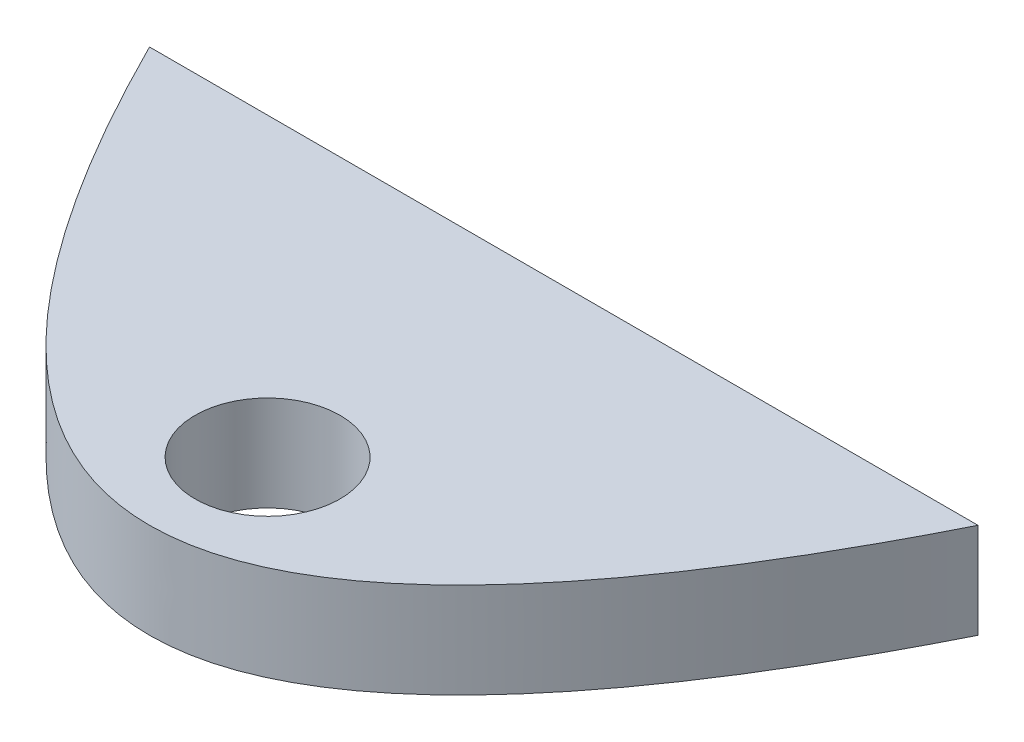
SolidWorks part; units mm, degrees
material "Custom Plastic (2)"
ref_plane "Front Plane" through (0, 0, 0) normal (0, 0, 1) x (1, 0, 0)
ref_plane "Top Plane" through (0, 0, 0) normal (0, 1, 0) x (1, 0, 0)
ref_plane "Right Plane" through (0, 0, 0) normal (1, 0, 0) x (0, 0, -1)
sketch "Sketch1" plane through (0, 0, 0) normal (0, 1, 0) x (1, 0, 0)
  line L0 (-200, 0) -> (200, 0)
  spline S0 degree 2 poles (-225.2396, 53.6645) (0, -453.6645) (225.2396, 53.6645) knots 0 0 0 1 1 1 construction
  spline S1 degree 2 poles (-200, 0) (0, -400) (200, 0) knots 0.056028 0.056028 0.056028 0.943972 0.943972 0.943972
extrude "Boss-Extrude1" add sketch "Sketch1" along normal blind 300
sketch "Sketch2" plane through (0, 300, 0) normal (0, 1, 0) x (1, 0, 0)
  line L0 (0, 200) -> (0, -200)
  line L2 (200, 0) -> (-200, 0) construction
  circle A0 centre (0, -143) radius 35
  parabola Q0 (-200, 0) -> (200, 0) focus (0, -150) apex (0, -200) construction
  point P4 (0, 0)
  dimension "D1" = 70
  dimension "D2" = 143
ref_plane "Plane1" through (0, 150, 0) normal (0, 1, 0) x (1, 0, 0)
sketch "Sketch3" plane through (0, 150, 0) normal (0, 1, 0) x (1, 0, 0)
  circle A0 centre (0, -143) radius 15.5
  dimension "D1" = 31
extrude "Cut-Extrude1" cut sketch "Sketch3" against normal blind 23 and the other way blind 23
ref_plane "Plane2" through (0, 173, 0) normal (0, 1, 0) x (1, 0, 0)
sketch "Sketch4" plane through (0, 173, 0) normal (0, 1, 0) x (1, 0, 0)
  circle A0 centre (0, -143) radius 35
extrude "Cut-Extrude3" cut sketch "Sketch4" along normal blind 300 contours A0
mirror "Mirror1" about plane through (0, 150, 0) normal (0, 1, 0) of "Cut-Extrude3"
sketch "Sketch5" plane through (0, 0, 0) normal (0, 0, -1) x (-1, 0, 0)
  line L0 (-200, 300) -> (200, 300) construction
  line L1 (-280.5284, 307.274) -> (269.8044, 307.274)
  line L2 (-280.5284, 307.274) -> (-280.5284, 46)
  line L3 (-280.5284, 46) -> (269.8044, 46)
  line L4 (269.8044, 307.274) -> (269.8044, 46)
  dimension "D1" = 254
extrude "Cut-Extrude4" cut sketch "Sketch5" against normal through all
